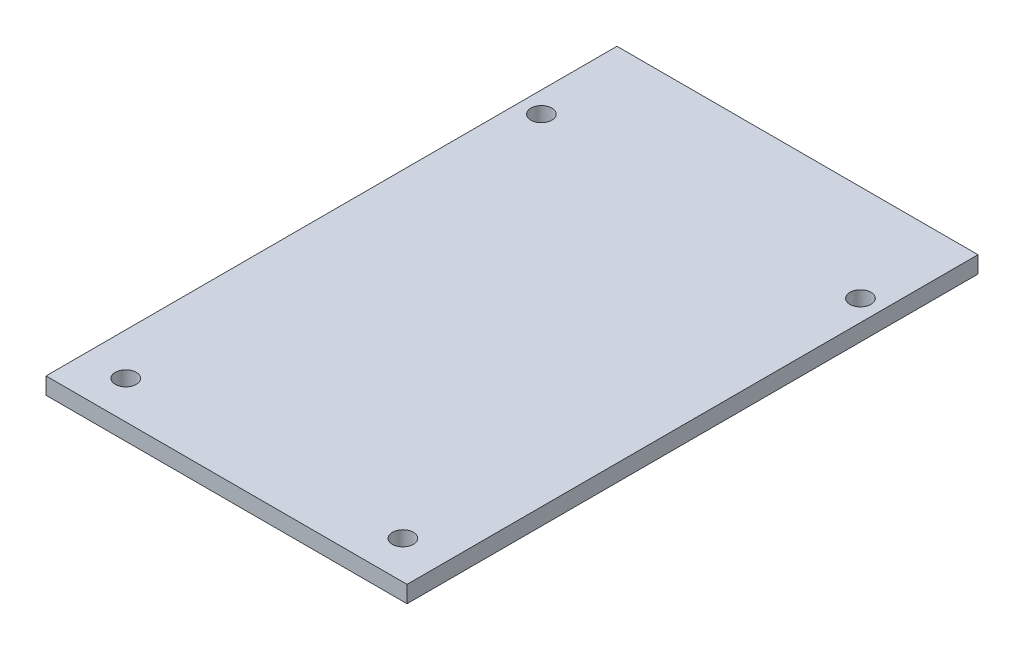
SolidWorks part; units mm, degrees
ref_plane "Front Plane" through (0, 0, 0) normal (0, 0, 1) x (1, 0, 0)
ref_plane "Top Plane" through (0, 0, 0) normal (0, 1, 0) x (1, 0, 0)
ref_plane "Right Plane" through (0, 0, 0) normal (1, 0, 0) x (0, 0, -1)
sketch "Sketch1" plane through (0, 0, 0) normal (0, 1, 0) x (1, 0, 0)
  line L1 (0, 0) -> (54.61, 0)
  line L2 (0, 0) -> (0, 86.36)
  line L3 (0, 86.36) -> (54.61, 86.36)
  line L4 (54.61, 0) -> (54.61, 86.36)
  dimension "D1" = 54.61
  dimension "D2" = 86.36
extrude "Boss-Extrude1" add sketch "Sketch1" along normal blind 2.54
sketch "Sketch2" plane through (0, 2.54, 0) normal (0, 1, 0) x (1, 0, 0)
  line L0 (0, 5.715) -> (54.61, 5.715) construction
  line L1 (0, 86.36) -> (0, 0) construction
  line L2 (54.61, 0) -> (54.61, 86.36) construction
  line L3 (51.435, 86.36) -> (51.435, 0) construction
  line L4 (54.61, 86.36) -> (0, 86.36) construction
  line L5 (0, 0) -> (54.61, 0) construction
  line L6 (0, 71.755) -> (54.61, 71.755) construction
  line L7 (3.175, 86.36) -> (3.175, 0) construction
  line L8 (6.35, 0) -> (6.35, 86.36) construction
  line L9 (48.26, 0) -> (48.26, 86.36) construction
  circle A0 centre (3.175, 71.755) radius 1.5875
  circle A1 centre (51.435, 71.755) radius 1.5875
  circle A2 centre (6.35, 5.715) radius 1.5875
  circle A3 centre (48.26, 5.715) radius 1.5875
  dimension "D7" = 3.175
  dimension "D8" = 3.175
  dimension "D9" = 3.175
  dimension "D10" = 3.175
  dimension "D1" = 14.605
  dimension "D2" = 5.715
  dimension "D3" = 3.175
  dimension "D4" = 3.175
  dimension "D5" = 6.35
  dimension "D6" = 41.91
extrude "Cut-Extrude1" cut sketch "Sketch2" against normal through all
equation "\"D8@Sketch2\"=\"D7@Sketch2\""
equation "\"D9@Sketch2\"=\"D7@Sketch2\""
equation "\"D10@Sketch2\"=\"D7@Sketch2\""
